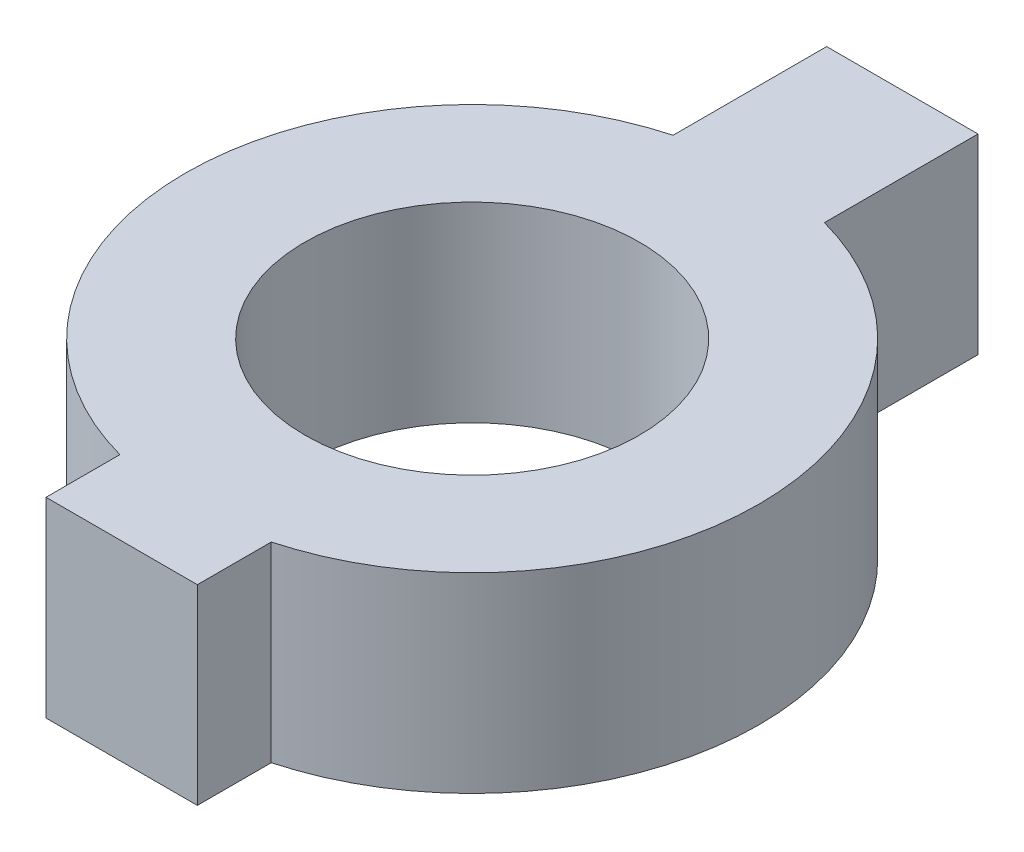
SolidWorks part; units mm, degrees
ref_plane "Plan de face" through (0, 0, 0) normal (0, 0, 1) x (1, 0, 0)
ref_plane "Plan de dessus" through (0, 0, 0) normal (0, 1, 0) x (1, 0, 0)
ref_plane "Plan de droite" through (0, 0, 0) normal (1, 0, 0) x (0, 0, -1)
sketch "Esquisse2" plane through (0, 0, 0) normal (0, 1, 0) x (1, 0, 0)
  line L1 (-4.75, -22) -> (4.75, -22)
  line L2 (-4.75, -22) -> (-4.75, -17.362)
  line L3 (-4.75, 27) -> (4.75, 27)
  line L4 (4.75, -22) -> (4.75, -17.362)
  line L5 (-4.75, 17.362) -> (-4.75, 27)
  line L7 (4.75, 17.362) -> (4.75, 27)
  circle A0 centre (0, 0) radius 18
  circle A1 centre (0, 0) radius 10.5
  point P8 (0, -22)
  point P9 (4.75, -17.362)
  point P10 (-4.75, -17.362)
  point P11 (4.75, 17.362)
  point P12 (-4.75, 17.362)
  point P13 (0, 0)
  point P14 (0, 0)
  point P15 (-4.75, -14.7864)
  point P18 (-68.199, 36.5329)
  point P19 (0, 0)
  point P22 (-88.676, 33.8768)
  point P23 (-86.905, 42.7317)
  dimension "D1" = 36
  dimension "D2" = 21
  dimension "D3" = 4.75
  dimension "D4" = 9.5
  dimension "D5" = 49
  dimension "D6" = 22
extrude "Boss.-Extru.1" add sketch "Esquisse2" along normal blind 12 contours A0 A1 | A0 L2 L1 L4 | A0 L7 L3 L5
